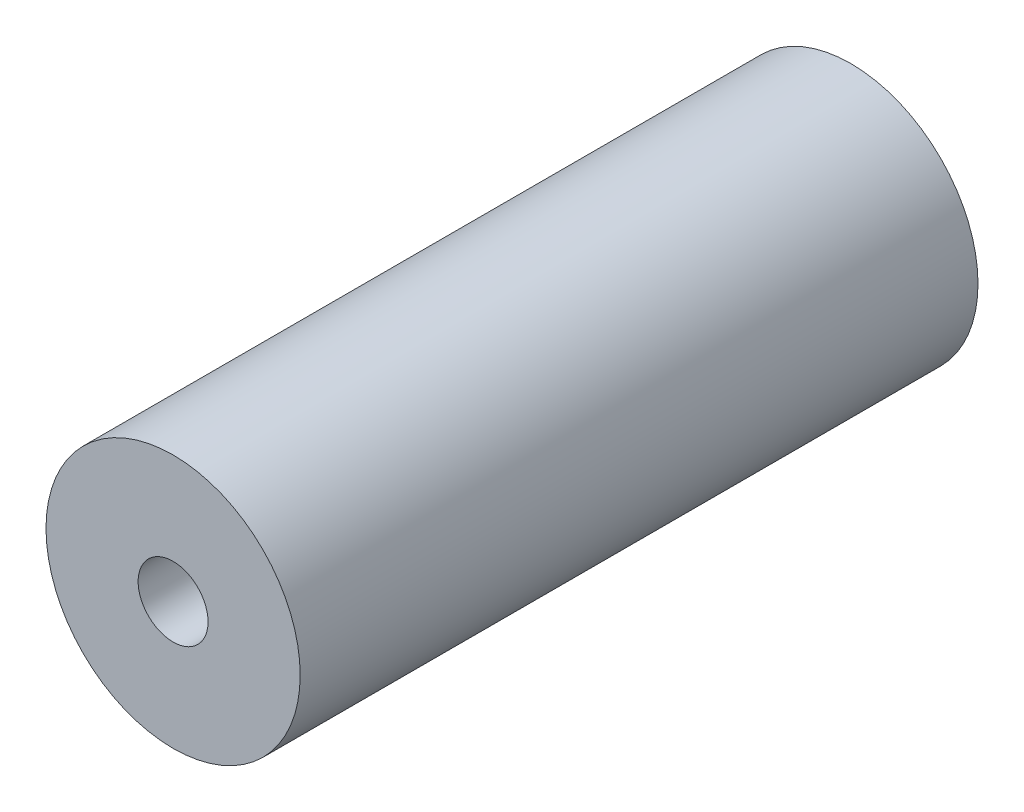
SolidWorks part; units mm, degrees
material "XC38"
ref_plane "Face" through (0, 0, 0) normal (0, 0, 1) x (1, 0, 0)
ref_plane "Dessus" through (0, 0, 0) normal (0, 1, 0) x (1, 0, 0)
ref_plane "Droite" through (0, 0, 0) normal (1, 0, 0) x (0, 0, -1)
sketch "Esquisse1" plane through (0, 0, 0) normal (0, 0, 1) x (1, 0, 0)
  circle A0 centre (0, 0) radius 6
  dimension "D1" = 12
extrude "Boss.-Extru.1" add sketch "Esquisse1" along normal mid plane 32
hole_wizard "Trou taraudé M41" positions "Esquisse5" profile "Esquisse4" tap size "M4" standard "ISO"
sketch "Esquisse5" plane through (0, 0, 16) normal (0, 0, 1) x (1, 0, 0)
  point P0 (0, 0)
sketch "Esquisse4" plane through (0, 0, 16) normal (1, 0, 0) x (0, -1, 0)
  line L0 (0, 0) -> (0, 12.4914)
  line L1 (0, 12.4914) -> (1.65, 11.5)
  line L2 (1.65, 11.5) -> (1.65, 0)
  line L5 (1.65, 0) -> (0, 0)
  line L10 (0, 12.4914) -> (-1.65, 11.5) construction
  line L11 (0, -6.35) -> (0, 107.95) construction
  dimension "Diamètre du trou pour taraudage" = 3.3
  dimension "Profondeur du trou pour taraudage" = 11.5
  dimension "Angle de pointe" = 118
cosmetic thread "Filetage de perçage1" parameters "D1"=8, "D2"=4
mirror "Symétrie1" about plane through (0, 0, 0) normal (0, 0, 1) of "Trou taraudé M41"
